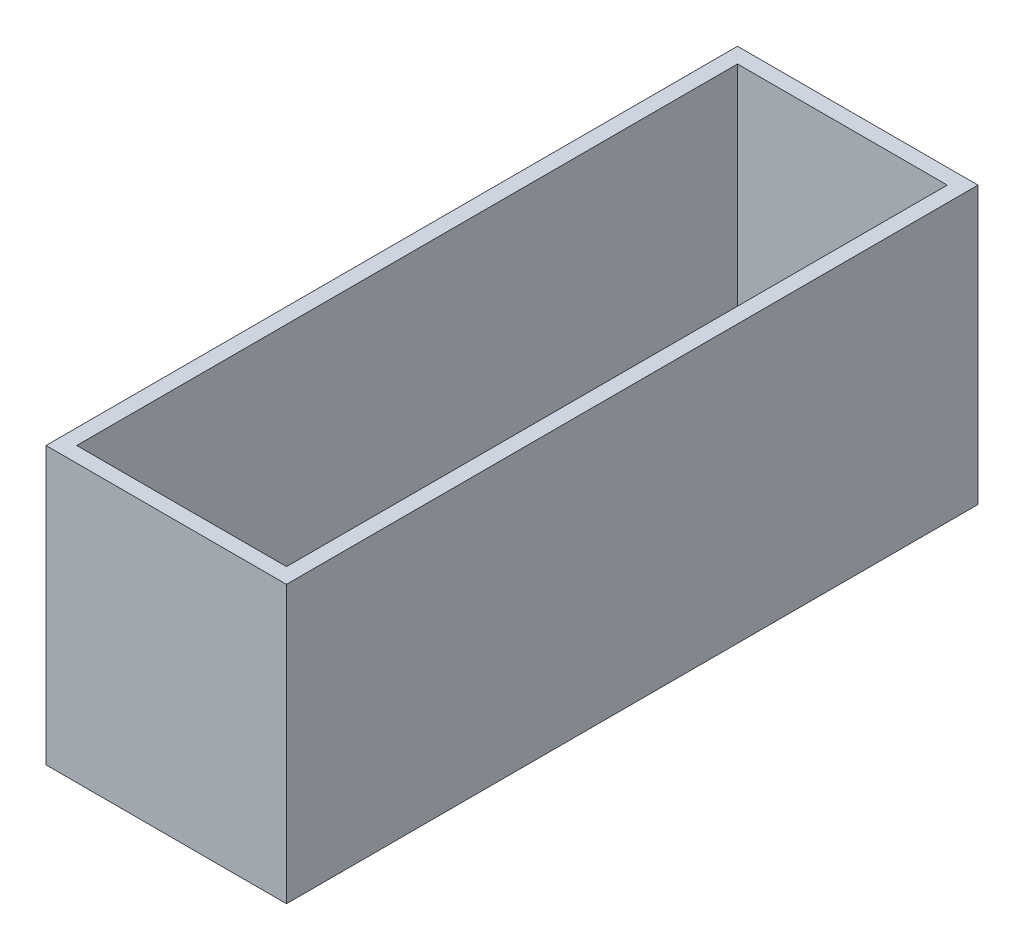
SolidWorks part; units mm, degrees
ref_plane "Front Plane" through (0, 0, 0) normal (0, 0, 1) x (1, 0, 0)
ref_plane "Top Plane" through (0, 0, 0) normal (0, 1, 0) x (1, 0, 0)
ref_plane "Right Plane" through (0, 0, 0) normal (1, 0, 0) x (0, 0, -1)
sketch "Sketch2" plane through (0, 0, 0) normal (0, 0, 1) x (1, 0, 0)
  line L1 (78.25, -90) -> (-78.25, -90)
  line L2 (78.25, -90) -> (78.25, 90)
  line L3 (78.25, 90) -> (-78.25, 90)
  line L4 (-78.25, -90) -> (-78.25, 90)
  line L5 (78.25, -90) -> (-78.25, 90) construction
  line L6 (78.25, 90) -> (-78.25, -90) construction
  point P0 (0, 0)
  dimension "D1" = 180
  dimension "D2" = 156.5
extrude "Boss-Extrude1" add sketch "Sketch2" along normal blind 450
sketch "Sketch3" plane through (0, 90, 0) normal (0, 1, 0) x (1, 0, 0)
  line L8 (68.25, -10) -> (-68.25, -10)
  line L9 (-68.25, -10) -> (-68.25, -440)
  line L10 (-68.25, -440) -> (68.25, -440)
  line L11 (68.25, -440) -> (68.25, -10)
  line L12 (68.25, -10) -> (-68.25, -10)
  line L13 (-68.25, -10) -> (-68.25, -440)
  line L14 (-68.25, -440) -> (68.25, -440)
  line L15 (68.25, -440) -> (68.25, -10)
  dimension "D1" = 10
extrude "Cut-Extrude1" cut sketch "Sketch3" against normal blind 160
